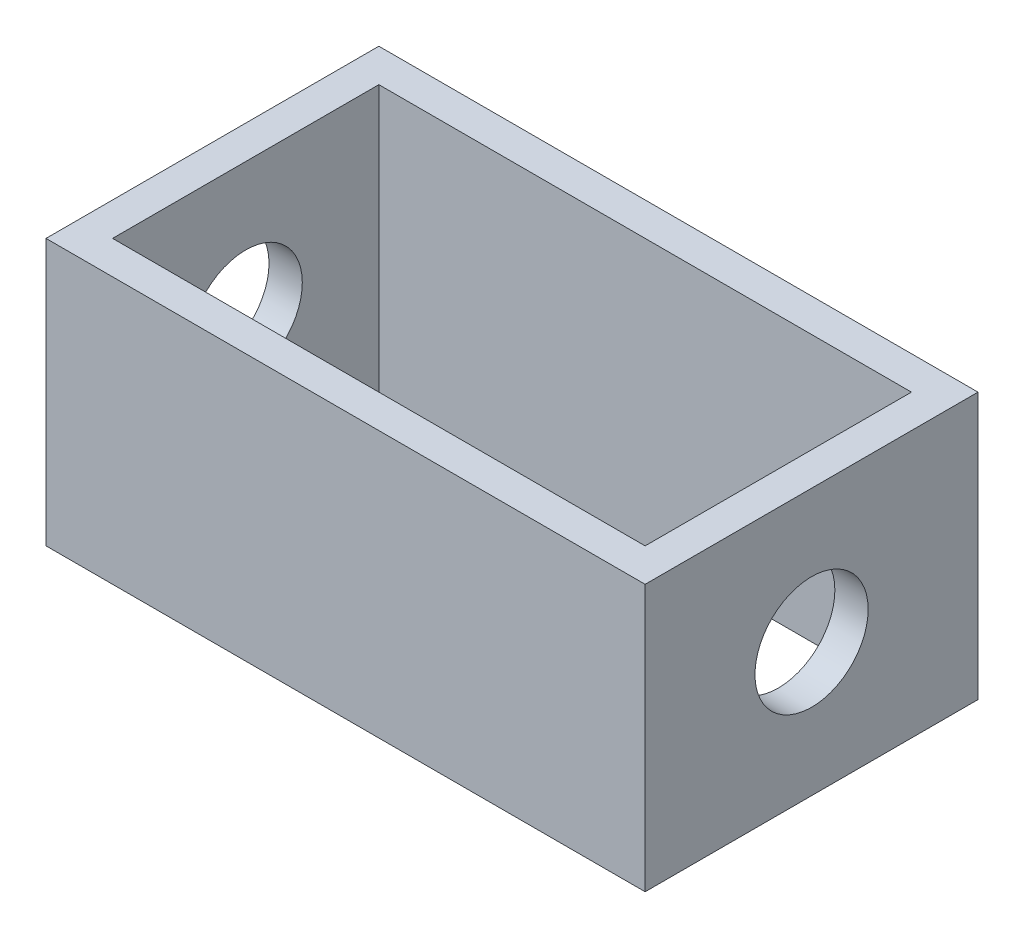
SolidWorks part; units mm, degrees
ref_plane "Front Plane" through (0, 0, 0) normal (0, 0, 1) x (1, 0, 0)
ref_plane "Top Plane" through (0, 0, 0) normal (0, 1, 0) x (1, 0, 0)
ref_plane "Right Plane" through (0, 0, 0) normal (1, 0, 0) x (0, 0, -1)
sketch "Sketch1" plane through (0, 0, 0) normal (0, 1, 0) x (1, 0, 0)
  line L1 (22.5, -12.5) -> (-22.5, -12.5)
  line L2 (22.5, -12.5) -> (22.5, 12.5)
  line L3 (22.5, 12.5) -> (-22.5, 12.5)
  line L4 (-22.5, -12.5) -> (-22.5, 12.5)
  line L5 (22.5, -12.5) -> (-22.5, 12.5) construction
  line L6 (22.5, 12.5) -> (-22.5, -12.5) construction
  line L7 (20, -10) -> (-20, -10)
  line L8 (20, -10) -> (20, 10)
  line L9 (20, 10) -> (-20, 10)
  line L10 (-20, -10) -> (-20, 10)
  line L11 (20, -10) -> (-20, 10) construction
  line L12 (20, 10) -> (-20, -10) construction
  point P0 (0, 0)
  point P6 (0, 0)
  dimension "D1" = 45
  dimension "D2" = 25
  dimension "D3" = 2.5
  dimension "D4" = 2.5
extrude "Boss-Extrude1" add sketch "Sketch1" along normal blind 2.5
sketch "Sketch2" plane through (0, 2.5, 0) normal (0, 1, 0) x (1, 0, 0)
  line L0 (22.5, 12.5) -> (-22.5, 12.5) construction
  line L1 (20, -10) -> (-20, -10)
  line L2 (20, -10) -> (20, 10)
  line L3 (20, 10) -> (-20, 10)
  line L4 (-20, -10) -> (-20, 10)
  line L5 (20, -10) -> (-20, 10) construction
  line L6 (20, 10) -> (-20, -10) construction
  line L7 (-22.5, 12.5) -> (-22.5, -12.5) construction
  line L9 (22.5, -12.5) -> (-22.5, -12.5)
  line L10 (22.5, -12.5) -> (22.5, 12.5)
  line L11 (22.5, 12.5) -> (-22.5, 12.5)
  line L12 (-22.5, -12.5) -> (-22.5, 12.5)
  line L13 (22.5, -12.5) -> (-22.5, 12.5) construction
  line L14 (22.5, 12.5) -> (-22.5, -12.5) construction
  point P0 (0, 0)
  point P10 (0, 0)
  dimension "D1" = 2.5
  dimension "D2" = 2.5
extrude "Boss-Extrude2" add sketch "Sketch2" along normal blind 17.5
sketch "Sketch3" plane through (22.5, 0, 0) normal (1, 0, 0) x (0, 0, -1)
  line L0 (0, 10) -> (0, 0) construction
  line L1 (0, 10) -> (0, 20) construction
  line L2 (-12.5, 20) -> (12.5, 20) construction
  circle A1 centre (0, 10) radius 4.25
  dimension "D1" = 8.5
extrude "Cut-Extrude1" cut sketch "Sketch3" against normal through all
